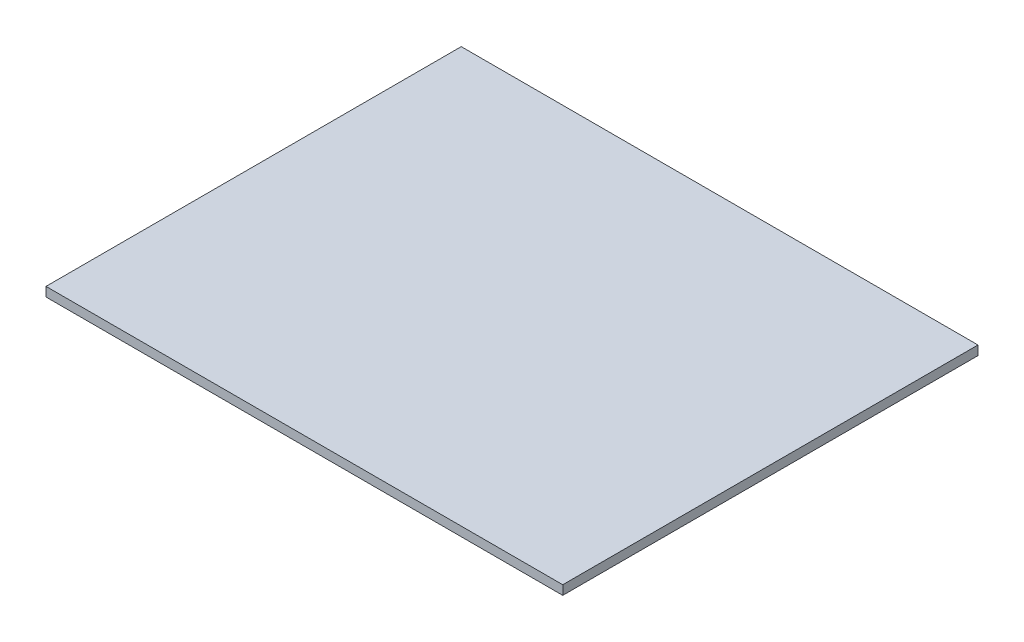
SolidWorks part; units mm, degrees
ref_plane "Front Plane" through (0, 0, 0) normal (0, 0, 1) x (1, 0, 0)
ref_plane "Top Plane" through (0, 0, 0) normal (0, 1, 0) x (1, 0, 0)
ref_plane "Right Plane" through (0, 0, 0) normal (1, 0, 0) x (0, 0, -1)
sketch "Sketch1" plane through (0, 0, 0) normal (0, 1, 0) x (1, 0, 0)
  line L1 (-28, 22.5) -> (28, 22.5)
  line L2 (-28, 22.5) -> (-28, -22.5)
  line L3 (-28, -22.5) -> (28, -22.5)
  line L4 (28, 22.5) -> (28, -22.5)
  line L5 (0, -22.5) -> (0, 22.5) construction
  line L6 (-28, 0) -> (28, 0) construction
  point P0 (0, 0)
  dimension "D1" = 56
  dimension "D2" = 45
extrude "Boss-Extrude1" add sketch "Sketch1" along normal blind 1
